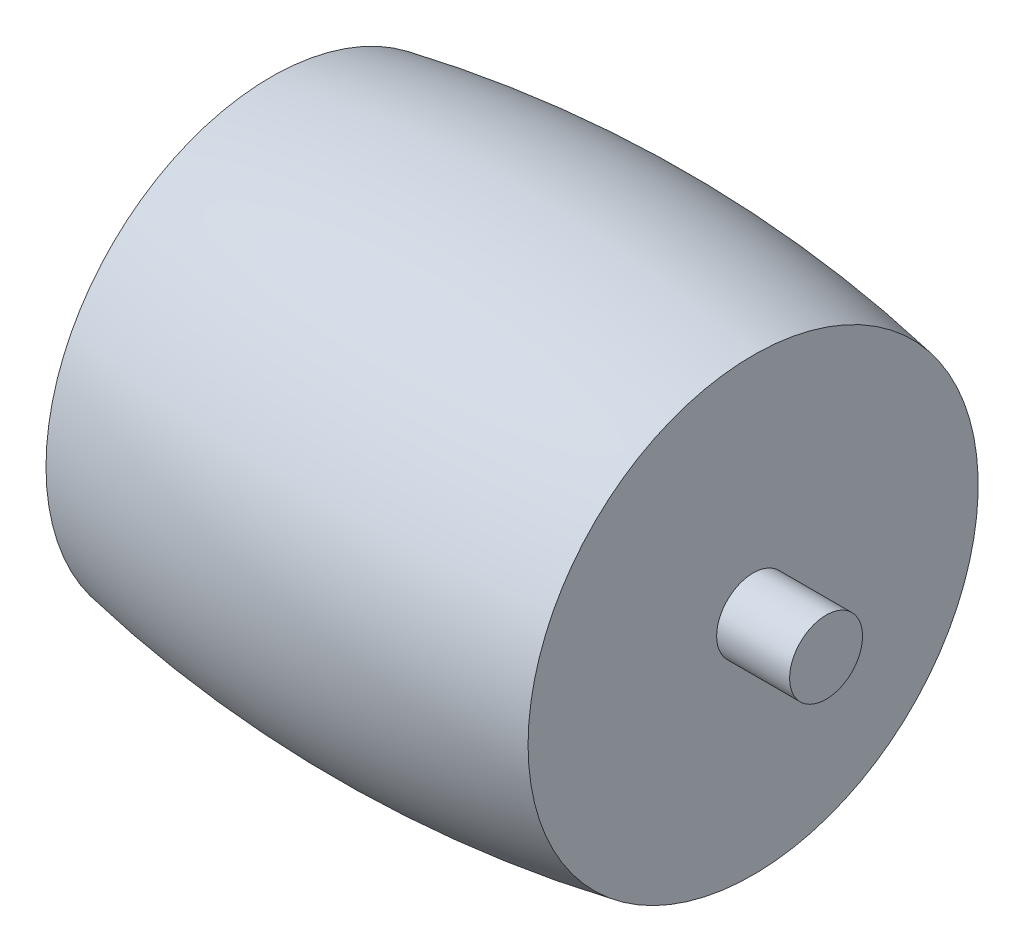
SolidWorks part; units mm, degrees
material "POLYURETHANE (11671)"
ref_plane "Front Plane" through (0, 0, 0) normal (0, 0, 1) x (1, 0, 0)
ref_plane "Top Plane" through (0, 0, 0) normal (0, 1, 0) x (1, 0, 0)
ref_plane "Right Plane" through (0, 0, 0) normal (1, 0, 0) x (0, 0, -1)
sketch "Sketch1" plane through (0, 0, 0) normal (0, 0, 1) x (1, 0, 0)
  line L1 (0, 50) -> (0, 40.5) construction
  line L2 (9.25, 49.1369) -> (9.25, 41.9)
  line L3 (-9.25, 40.5) -> (-12.05, 40.5)
  line L4 (-9.25, 40.5) -> (9.25, 40.5)
  line L7 (-12.05, 41.9) -> (-12.05, 40.5)
  line L8 (9.25, 41.9) -> (12.05, 41.9)
  line L9 (-9.25, 41.9) -> (-12.05, 41.9)
  line L10 (9.25, 40.5) -> (12.05, 40.5)
  line L11 (12.05, 41.9) -> (12.05, 40.5)
  line L12 (-9.25, 49.1369) -> (-9.25, 41.9)
  arc A0 (9.25, 49.1369) -> (-9.25, 49.1369) centre (0, 0) ccw
  dimension "D1" = 100
  dimension "D2" = 18.5
  dimension "D3" = 9.5
  dimension "D4" = 2.8
  dimension "D5" = 1.4
revolve "Revolve1" add sketch "Sketch1" angle 360 about L4
